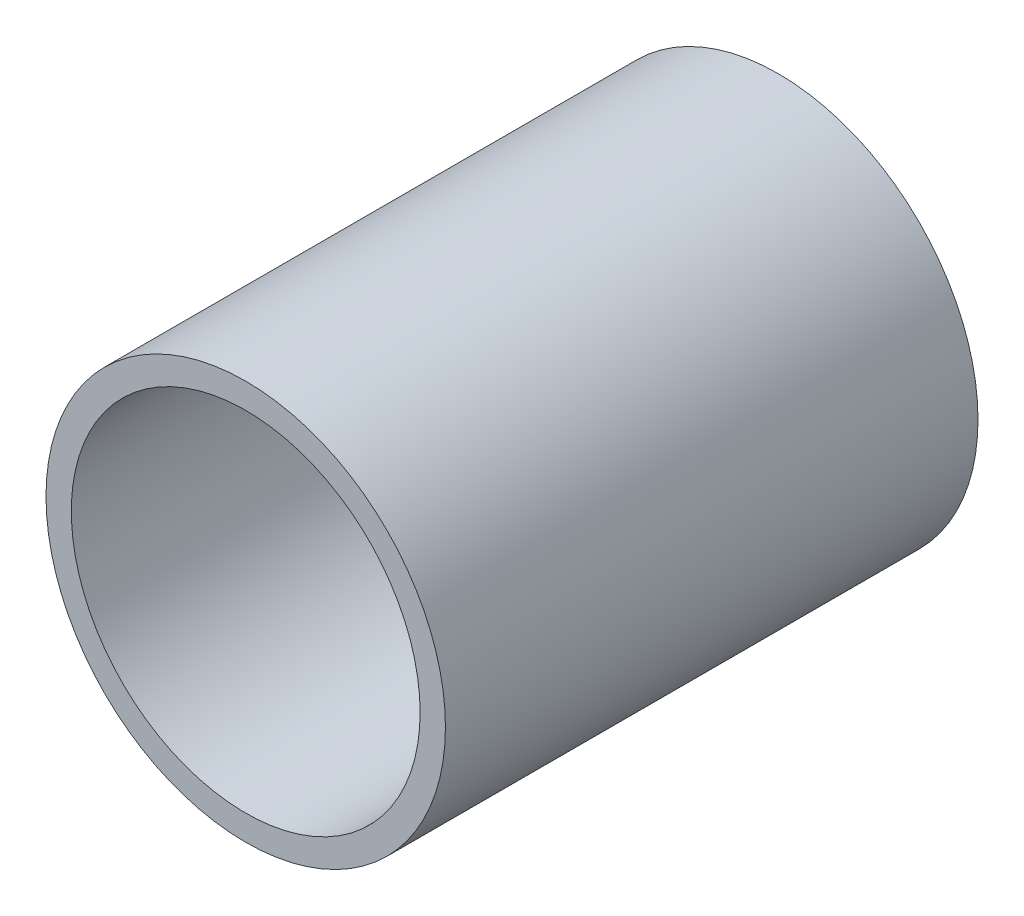
SolidWorks part; units mm, degrees
ref_plane "Front Plane" through (0, 0, 0) normal (0, 0, 1) x (1, 0, 0)
ref_plane "Top Plane" through (0, 0, 0) normal (0, 1, 0) x (1, 0, 0)
ref_plane "Right Plane" through (0, 0, 0) normal (1, 0, 0) x (0, 0, -1)
sketch "Sketch1" plane through (0, 0, 0) normal (0, 0, 1) x (1, 0, 0)
  circle A0 centre (0, 0) radius 19.05
  circle A1 centre (0, 0) radius 16.637
  dimension "D1" = 33.274
  dimension "D2" = 38.1
extrude "Extrude1" add sketch "Sketch1" along normal blind 50.8
